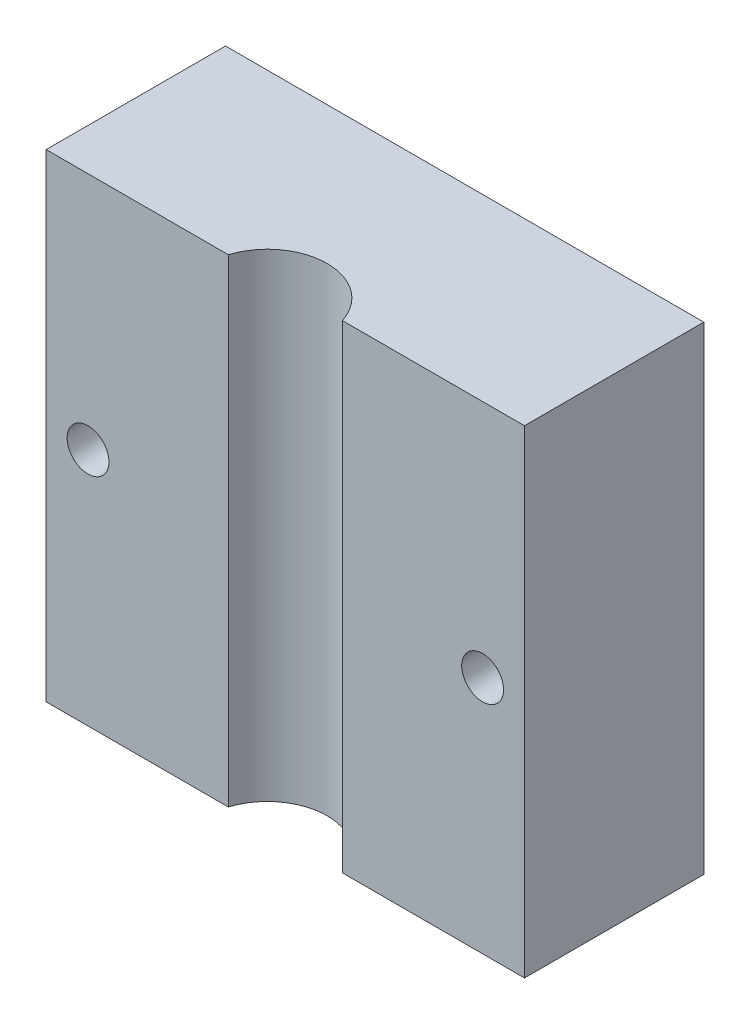
SolidWorks part; units mm, degrees
ref_plane "Front Plane" through (0, 0, 0) normal (0, 0, 1) x (1, 0, 0)
ref_plane "Top Plane" through (0, 0, 0) normal (0, 1, 0) x (1, 0, 0)
ref_plane "Right Plane" through (0, 0, 0) normal (1, 0, 0) x (0, 0, -1)
sketch "Sketch1" plane through (0, 0, 0) normal (0, 0, 1) x (1, 0, 0)
  line L1 (-20, 20) -> (20, 20)
  line L2 (-20, 20) -> (-20, -20)
  line L3 (-20, -20) -> (20, -20)
  line L4 (20, 20) -> (20, -20)
  line L5 (-20, 20) -> (20, -20) construction
  line L6 (-20, -20) -> (20, 20) construction
  point P0 (0, 0)
  dimension "D1" = 40
  dimension "D2" = 40
extrude "Boss-Extrude1" add sketch "Sketch1" along normal blind 15
sketch "Sketch2" plane through (0, 0, 15) normal (0, 0, 1) x (1, 0, 0)
  line L0 (20, 20) -> (-20, 20) construction
  line L1 (-20, 20) -> (-20, -20) construction
  line L2 (20, -20) -> (20, 20) construction
  circle A0 centre (-16.5, 0) radius 1.75
  circle A1 centre (16.5, 0) radius 1.75
  dimension "D3" = 3.5
  dimension "D4" = 3.5
  dimension "D1" = 20
  dimension "D2" = 20
  dimension "D5" = 3.5
  dimension "D6" = 3.5
extrude "Cut-Extrude1" cut sketch "Sketch2" against normal through all
sketch "Sketch3" plane through (0, 20, 0) normal (0, 1, 0) x (1, 0, 0)
  line L0 (20, -15) -> (-20, -15) construction
  line L2 (20, -15) -> (20, 0) construction
  circle A0 centre (0, -16.5) radius 5
  point P7 (20, -11.8628)
  dimension "D1" = 10
  dimension "D2" = 1.5
  dimension "D3" = 20
extrude "Cut-Extrude2" cut sketch "Sketch3" against normal through all
